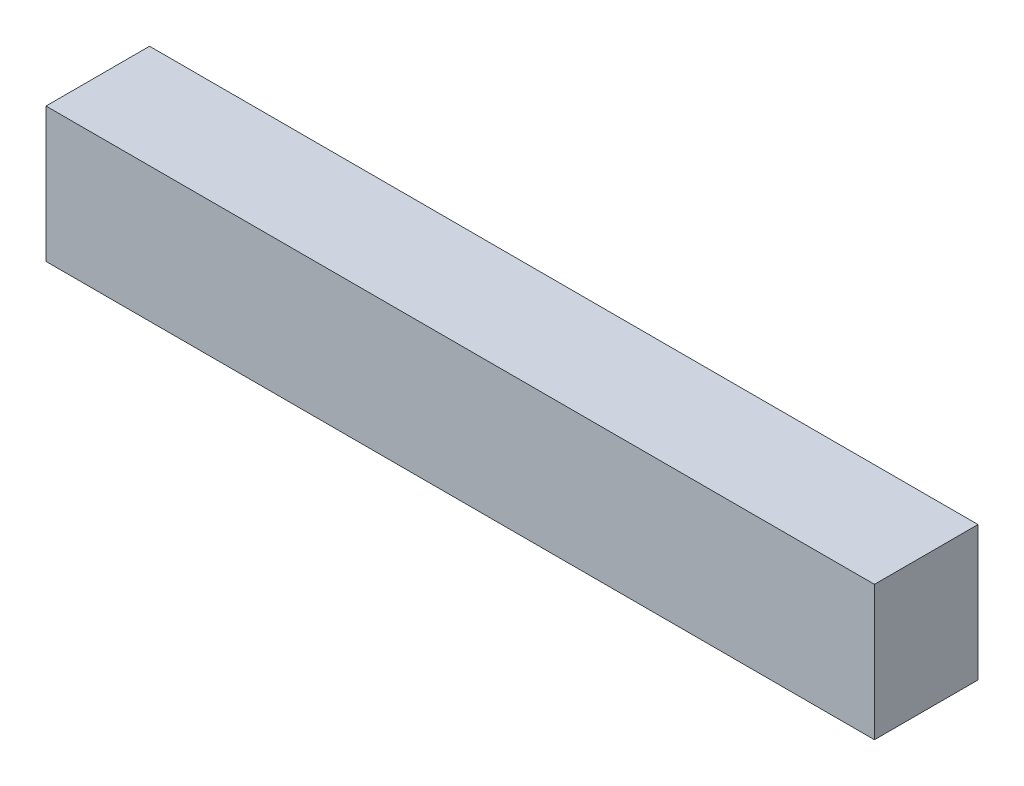
SolidWorks part; units mm, degrees
ref_plane "Front Plane" through (0, 0, 0) normal (0, 0, 1) x (1, 0, 0)
ref_plane "Top Plane" through (0, 0, 0) normal (0, 1, 0) x (1, 0, 0)
ref_plane "Right Plane" through (0, 0, 0) normal (1, 0, 0) x (0, 0, -1)
sketch "Sketch2" plane through (0, 0, 0) normal (0, 0, 1) x (1, 0, 0)
  line L1 (-20, 3.25) -> (20, 3.25)
  line L2 (-20, 3.25) -> (-20, -3.25)
  line L3 (-20, -3.25) -> (20, -3.25)
  line L4 (20, 3.25) -> (20, -3.25)
  line L5 (-20, 3.25) -> (20, -3.25) construction
  line L6 (-20, -3.25) -> (20, 3.25) construction
  point P0 (0, 0)
  dimension "D1" = 6.5
  dimension "D2" = 40
extrude "Boss-Extrude1" add sketch "Sketch2" along normal blind 5
